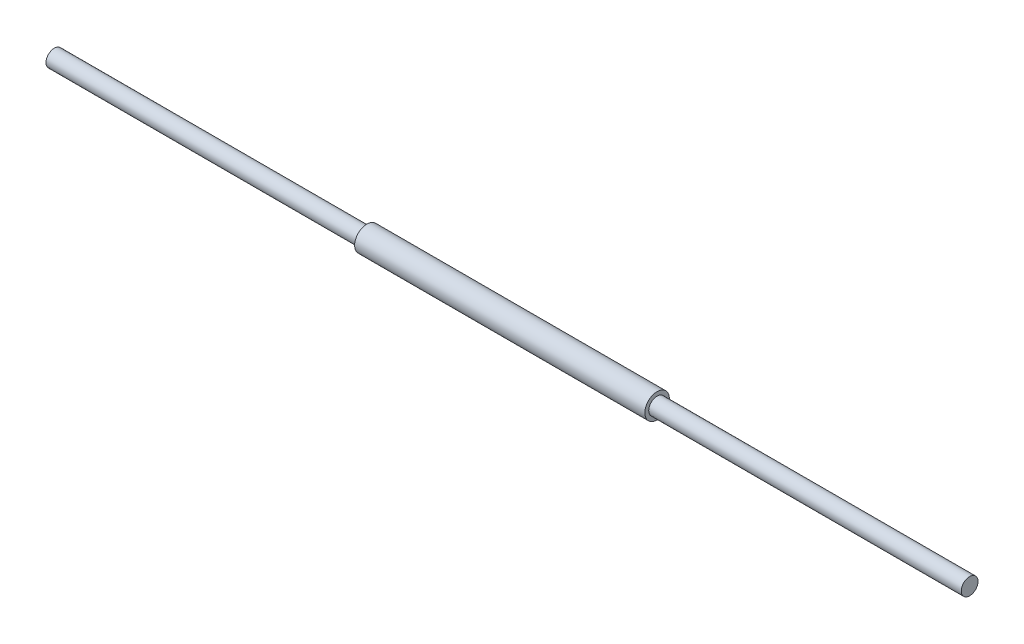
SolidWorks part; units mm, degrees
material "AISI 1020"
ref_plane "Front Plane" through (0, 0, 0) normal (0, 0, 1) x (1, 0, 0)
ref_plane "Top Plane" through (0, 0, 0) normal (0, 1, 0) x (1, 0, 0)
ref_plane "Right Plane" through (0, 0, 0) normal (1, 0, 0) x (0, 0, -1)
sketch "Sketch1" plane through (0, 0, 0) normal (0, 0, 1) x (1, 0, 0)
  line L0 (-260.35, 0) -> (260.35, 0) construction
  line L1 (-260.35, 4.7625) -> (-82.55, 4.7625)
  line L2 (-260.35, 4.7625) -> (-260.35, 0)
  line L3 (260.35, 4.7625) -> (260.35, 0)
  line L4 (260.35, 0) -> (-260.35, 0)
  line L5 (-82.55, 4.7625) -> (-82.55, 6.985)
  line L6 (-82.55, 6.985) -> (82.55, 6.985)
  line L7 (82.55, 6.985) -> (82.55, 4.7625)
  line L8 (82.55, 4.7625) -> (260.35, 4.7625)
  point P4 (0, 0)
  point P8 (0, 6.985)
  dimension "D1" = 520.7
  dimension "D2" = 9.525
  dimension "D3" = 165.1
  dimension "D4" = 6.985
revolve "Revolve1" add sketch "Sketch1" angle 360 about L0
equation "\"A\"= 20.5in"
equation "\"B\"= 6.5in"
equation "\"C\"= 36deg"
equation "\"D1@Sketch1\"=\"A\""
equation "\"D3@Sketch1\"=\"B\""
